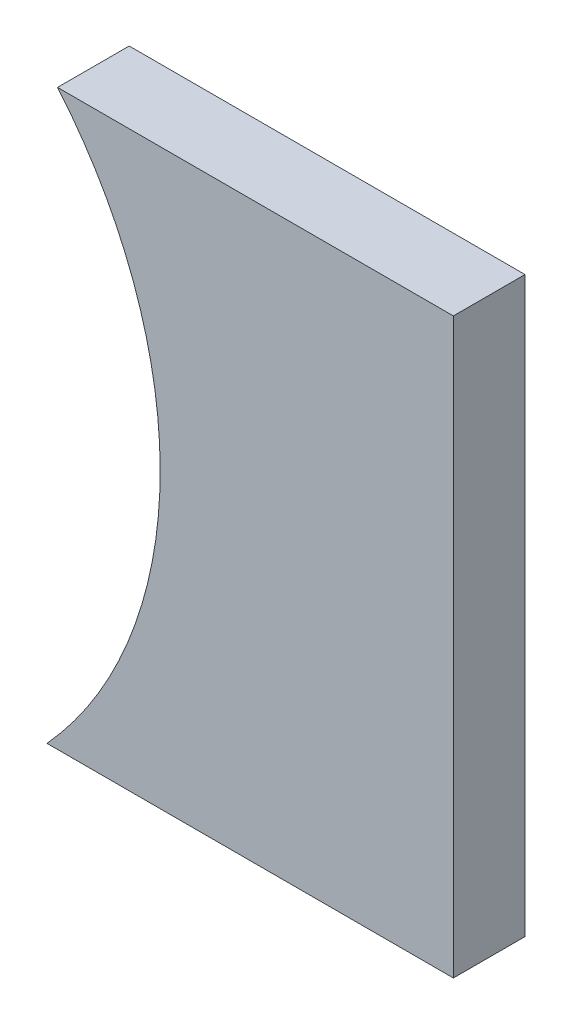
SolidWorks part; units mm, degrees
material "1.7218 (25CrMo4)"
ref_plane "Płaszczyzna XY" through (0, 0, 0) normal (0, 0, 1) x (1, 0, 0)
ref_plane "Płaszczyzna XZ" through (0, 0, 0) normal (0, 1, 0) x (1, 0, 0)
ref_plane "Płaszczyzna YZ" through (0, 0, 0) normal (1, 0, 0) x (0, 0, -1)
sketch "Szkic1" plane through (0, 0, 0) normal (0, 0, 1) x (1, 0, 0)
  line L0 (39.6607, 7.348) -> (39.9982, -8.652)
  line L4 (39.9982, -8.652) -> (67.3677, -8.652)
  line L5 (67.3677, 7.348) -> (39.6607, 7.348)
  line L6 (67.3677, -8.652) -> (67.3677, 7.348)
  line L7 (39.9982, -8.652) -> (67.3677, -8.652)
  line L8 (67.3677, 7.348) -> (39.6607, 7.348)
  line L9 (67.3677, -8.652) -> (67.3677, 7.348)
  spline S1 degree 3 poles (39.6607, 7.348) (43.565, 2.6928) (43.9042, -3.5606) (39.9982, -8.652) knots 0.687953 0.687953 0.687953 0.687953 0.866139 0.866139 0.866139 0.866139 weights 0.607906 0.497536 0.471834 0.530799
  dimension "D1" = 0
extrude "Dodanie-wyciągnięcie1" add sketch "Szkic1" against normal blind 2
sketch "Szkic2" plane through (0, 0, 0) normal (0, 0, 1) x (1, 0, 0)
  line L0 (62.3677, 7.348) -> (62.3677, -8.652)
  line L3 (67.3677, 7.348) -> (39.6607, 7.348)
  line L4 (39.9982, -8.652) -> (67.3677, -8.652)
  line L5 (67.3677, -8.652) -> (67.3677, 7.348)
  line L6 (67.3677, 7.348) -> (39.6607, 7.348)
  line L7 (39.9982, -8.652) -> (67.3677, -8.652)
  line L8 (67.3677, -8.652) -> (67.3677, 7.348)
  line L11 (39.6607, 7.348) -> (39.9982, -8.652)
  line L12 (39.6607, 7.348) -> (39.9982, -8.652)
  dimension "D2" = 5
  dimension "D1" = 0
extrude "Wytnij-wyciągnięcie1" cut sketch "Szkic2" against normal blind 5 contours L7 L8 L6 L0
sketch "Szkic3" plane through (0, 0, 0) normal (0, 0, 1) x (1, 0, 0)
  line L0 (39.6607, 7.348) -> (39.9982, -8.652)
  line L1 (39.9982, -8.652) -> (48.1252, -8.652)
  line L2 (39.9982, -8.652) -> (62.3677, -8.652) construction
  line L3 (39.6607, 7.348) -> (49.29, 7.348)
  line L4 (62.3677, 7.348) -> (39.6607, 7.348) construction
  line L5 (62.3677, 7.348) -> (62.3677, -8.652) construction
  arc A0 (48.1252, -8.652) -> (49.29, 7.348) centre (39.4885, 0.0192) ccw
  dimension "D1" = 12.2385
  dimension "D2" = 13.0777
  dimension "D3" = 14.2425
extrude "Wytnij-wyciągnięcie2" cut sketch "Szkic3" against normal blind 10
sketch "Szkic4" plane through (0, 0, 0) normal (0, 0, 1) x (1, 0, 0)
  line L0 (48.1252, -8.652) -> (51.0272, -8.652)
  line L1 (48.1252, -8.652) -> (62.3677, -8.652) construction
  line L2 (49.29, 7.348) -> (51.3221, 7.348)
  line L3 (62.3677, 7.348) -> (49.29, 7.348) construction
  line L4 (49.29, 7.348) -> (48.1252, -8.652)
  arc A0 (51.3221, 7.348) -> (51.0272, -8.652) centre (42.0494, -0.4838) cw
  dimension "D1" = 12.1375
  dimension "D2" = 2.902
  dimension "D3" = 3.1969
extrude "Wytnij-wyciągnięcie3" cut sketch "Szkic4" against normal blind 10
